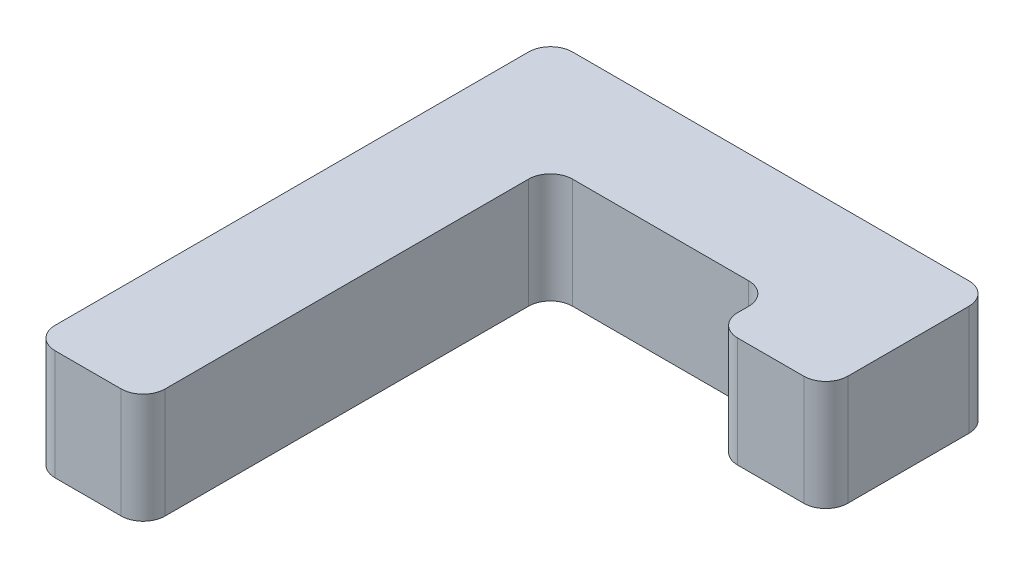
SolidWorks part; units mm, degrees
ref_plane "Front Plane" through (0, 0, 0) normal (0, 0, 1) x (1, 0, 0)
ref_plane "Top Plane" through (0, 0, 0) normal (0, 1, 0) x (1, 0, 0)
ref_plane "Right Plane" through (0, 0, 0) normal (1, 0, 0) x (0, 0, -1)
sketch "Sketch1" plane through (0, 0, 0) normal (0, 1, 0) x (1, 0, 0)
  line L0 (0, 0) -> (0, 59.69)
  line L1 (0, 59.69) -> (50.8, 59.69)
  line L2 (50.8, 59.69) -> (50.8, 40.64)
  line L3 (50.8, 40.64) -> (38.1, 40.64)
  line L4 (38.1, 40.64) -> (38.1, 46.99)
  line L5 (38.1, 46.99) -> (12.7, 46.99)
  line L6 (12.7, 46.99) -> (12.7, 0)
  line L7 (12.7, 0) -> (0, 0)
  dimension "D1" = 25.4
  dimension "D2" = 50.8
  dimension "D3" = 12.7
  dimension "D4" = 12.7
  dimension "D5" = 19.05
  dimension "D6" = 59.69
extrude "Boss-Extrude1" add sketch "Sketch1" along normal blind 12.7
fillet "Fillet1" radius 2.54 8 edges at (50.8, 6.35, -59.69) (38.1, 6.35, -46.99) (50.8, 6.35, -40.64) (38.1, 6.35, -40.64) (12.7, 6.35, 0) (0, 6.35, 0) (12.7, 6.35, -46.99) (0, 6.35, -59.69)
ref_plane "Plane1" through (25.4, 0, 0) normal (1, 0, 0) x (0, 0, -1)
